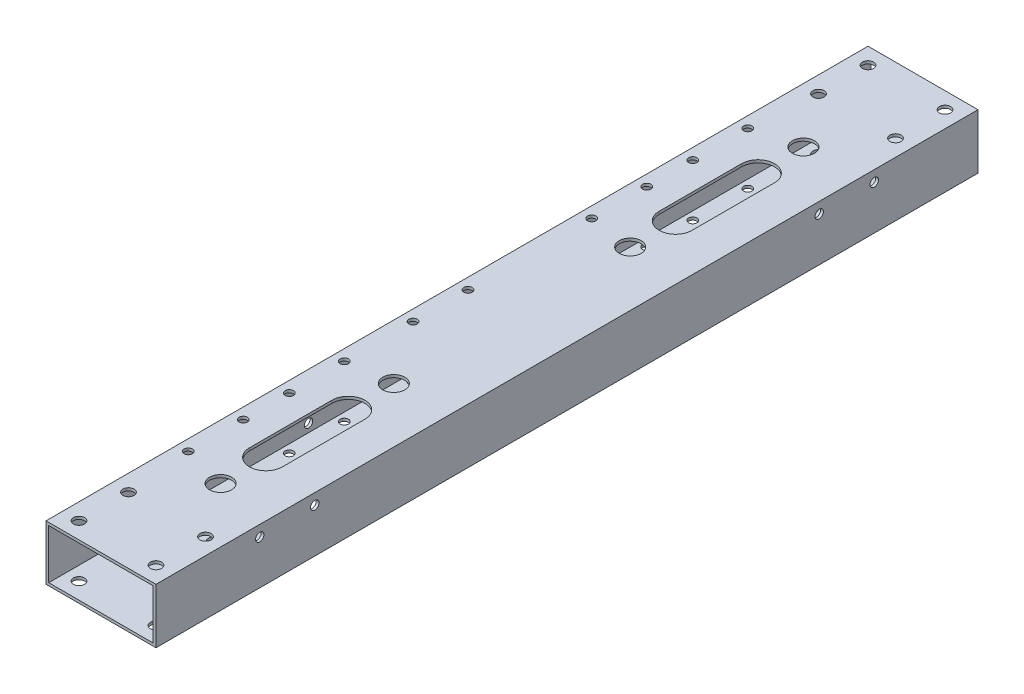
SolidWorks part; units mm, degrees
material "6063-T5"
ref_plane "前视基准面" through (0, 0, 0) normal (0, 0, 1) x (1, 0, 0)
ref_plane "上视基准面" through (0, 0, 0) normal (0, 1, 0) x (1, 0, 0)
ref_plane "右视基准面" through (0, 0, 0) normal (1, 0, 0) x (0, 0, -1)
other "Configuration Table"
sketch "草图1" plane through (0, 0, 0) normal (0, 0, 1) x (1, 0, 0)
  line L1 (-20, -10) -> (20, -10)
  line L2 (-20, -10) -> (-20, 10)
  line L3 (-20, 10) -> (20, 10)
  line L4 (20, -10) -> (20, 10)
  line L5 (-20, -10) -> (20, 10) construction
  line L6 (-20, 10) -> (20, -10) construction
  point P0 (0, 0)
  dimension "D1" = 40
  dimension "D2" = 20
extrude "凸台-拉伸1" add sketch "草图1" along normal mid plane 299
sketch "草图2" plane through (0, 0, 0) normal (0, 0, 1) x (1, 0, 0)
  line L8 (19, -9) -> (19, 9)
  line L9 (19, 9) -> (-19, 9)
  line L10 (-19, 9) -> (-19, -9)
  line L11 (-19, -9) -> (19, -9)
  line L12 (19, -9) -> (19, 9)
  line L13 (19, 9) -> (-19, 9)
  line L14 (-19, 9) -> (-19, -9)
  line L15 (-19, -9) -> (19, -9)
  dimension "D1" = 1
extrude "切除-拉伸1" cut sketch "草图2" against normal mid plane 299
sketch "草图4" plane through (-20, 0, 0) normal (-1, 0, 0) x (0, 0, 1)
  circle A0 centre (55, -6) radius 1.525 construction
  circle A1 centre (55, 6) radius 1.525 construction
  circle A2 centre (35, 6) radius 1.525 construction
  circle A3 centre (35, -6) radius 1.525 construction
  circle A4 centre (10, -6) radius 1.525 construction
  circle A5 centre (10, 6) radius 1.525 construction
  circle A6 centre (-10, 6) radius 1.525 construction
  circle A7 centre (-10, -6) radius 1.525 construction
  circle A8 centre (-35, 6) radius 1.525 construction
  circle A9 centre (-55, -6) radius 1.525 construction
  circle A10 centre (-55, 6) radius 1.525 construction
  circle A11 centre (-35, -6) radius 1.525 construction
  circle A12 centre (55, -6) radius 1.525
  circle A13 centre (55, 6) radius 1.525
  circle A14 centre (35, 6) radius 1.525
  circle A15 centre (35, -6) radius 1.525
  circle A16 centre (10, -6) radius 1.525
  circle A17 centre (10, 6) radius 1.525
  circle A18 centre (-10, 6) radius 1.525
  circle A19 centre (-10, -6) radius 1.525
  circle A20 centre (-35, 6) radius 1.525
  circle A21 centre (-55, -6) radius 1.525
  circle A22 centre (-55, 6) radius 1.525
  circle A23 centre (-35, -6) radius 1.525
extrude "切除-拉伸2" cut sketch "草图4" against normal blind 10
sketch "草图5" plane through (0, -10, 0) normal (0, -1, 0) x (1, 0, 0)
  line L0 (-20, 149.5) -> (20, 149.5) construction
  line L1 (-20, 149.5) -> (-20, -149.5) construction
  line L2 (-20, -149.5) -> (20, -149.5) construction
  circle A0 centre (-16, 65) radius 1.525
  circle A1 centre (-16, 45) radius 1.525
  circle A2 centre (-16, 20) radius 1.525
  circle A3 centre (-16, 0) radius 1.525
  circle A4 centre (-16, -45) radius 1.525
  circle A5 centre (-16, -65) radius 1.525
  dimension "D1" = 3.05
  dimension "D2" = 20
  dimension "D3" = 20
  dimension "D4" = 20
  dimension "D5" = 84.5
  dimension "D6" = 4
  dimension "D7" = 84.5
  dimension "D8" = 129.5
extrude "切除-拉伸3" cut sketch "草图5" against normal through all
sketch "草图6" plane through (0, 10, 0) normal (0, 1, 0) x (1, 0, 0)
  circle A0 centre (-16, -81.75) radius 1.525
  circle A1 centre (-16, -101.75) radius 1.525
  dimension "D1" = 3.05
extrude "切除-拉伸4" cut sketch "草图6" against normal through all
sketch "草图7" plane through (-20, 0, 0) normal (-1, 0, 0) x (0, 0, 1)
  line L0 (149.5, 10) -> (149.5, -10) construction
  line L1 (149.5, 10) -> (-149.5, 10) construction
  circle A0 centre (91.75, 6) radius 1.525
  circle A1 centre (111.75, 6) radius 1.525
  dimension "D1" = 3.05
  dimension "D2" = 20
  dimension "D3" = 37.75
  dimension "D4" = 4
extrude "切除-拉伸5" cut sketch "草图7" against normal through all both
sketch "草图9" plane through (0, -10, 0) normal (0, -1, 0) x (1, 0, 0)
  circle A0 centre (14, -125.5) radius 2.025
  circle A1 centre (-14, -125.5) radius 2.025
  circle A2 centre (14, -143.5) radius 2.025
  circle A3 centre (-14, -143.5) radius 2.025
  dimension "D1" = 4.05
extrude "切除-拉伸6" cut sketch "草图9" against normal through all both and the other way through all
sketch "草图10" plane through (0, 10, 0) normal (0, 1, 0) x (1, 0, 0)
  line L0 (0, -89.5) -> (0, -59.5) construction
  line L1 (-6, -89.5) -> (-6, -59.5)
  line L2 (6, -89.5) -> (6, -59.5)
  line L3 (0, 0) -> (20, 0) construction
  line L4 (20, -149.5) -> (20, 149.5) construction
  line L6 (0, 89.5) -> (0, 59.5) construction
  line L7 (-6, 89.5) -> (-6, 59.5)
  line L8 (6, 89.5) -> (6, 59.5)
  line L9 (20, -149.5) -> (-20, -149.5) construction
  arc A0 (-6, -89.5) -> (6, -89.5) centre (0, -89.5) ccw
  arc A1 (6, -59.5) -> (-6, -59.5) centre (0, -59.5) ccw
  arc A2 (-6, 89.5) -> (6, 89.5) centre (0, 89.5) cw
  arc A3 (6, 59.5) -> (-6, 59.5) centre (0, 59.5) cw
  point P3 (0, -74.5)
  point P16 (0, 74.5)
  dimension "D1" = 6
  dimension "D2" = 75
  dimension "D3" = 30
extrude "切除-拉伸7" cut sketch "草图10" against normal through all both and the other way through all
sketch "草图11" plane through (0, -10, 0) normal (0, -1, 0) x (1, 0, 0)
  line L0 (6, -74.5) -> (-6, -74.5) construction
  line L1 (6, -59.5) -> (6, -89.5) construction
  line L2 (-6, -89.5) -> (-6, -59.5) construction
  circle A0 centre (0, -43) radius 4
  circle A1 centre (0, -106) radius 4
  dimension "D2" = 8
  dimension "D1" = 63
extrude "切除-拉伸8" cut sketch "草图11" against normal through all both and the other way through all
mirror "镜向1" about plane through (0, 0, 0) normal (0, 0, 1) of "切除-拉伸8"
mirror "镜向2" about plane through (0, 0, 0) normal (0, 0, 1) of "切除-拉伸6"
sketch "草图12" plane through (0, 10, 0) normal (0, 1, 0) x (1, 0, 0)
  line L0 (-20, -149.5) -> (-20, 149.5) construction
  line L1 (20, 149.5) -> (-20, 149.5) construction
  circle A0 centre (-16, 81.75) radius 1.525
  circle A1 centre (-16, 101.75) radius 1.525
  dimension "D1" = 3.05
  dimension "D2" = 4
  dimension "D3" = 20
  dimension "D4" = 47.75
extrude "切除-拉伸9" cut sketch "草图12" against normal through all both and the other way through all
sketch "草图13" plane through (-20, 0, 0) normal (-1, 0, 0) x (0, 0, 1)
  line L0 (149.5, 10) -> (-149.5, 10) construction
  line L1 (-149.5, 10) -> (-149.5, -10) construction
  circle A0 centre (-91.75, 6) radius 1.525
  circle A1 centre (-111.75, 6) radius 1.525
  dimension "D1" = 3.05
  dimension "D2" = 4
  dimension "D3" = 20
  dimension "D4" = 37.75
extrude "切除-拉伸10" cut sketch "草图13" against normal through all both
